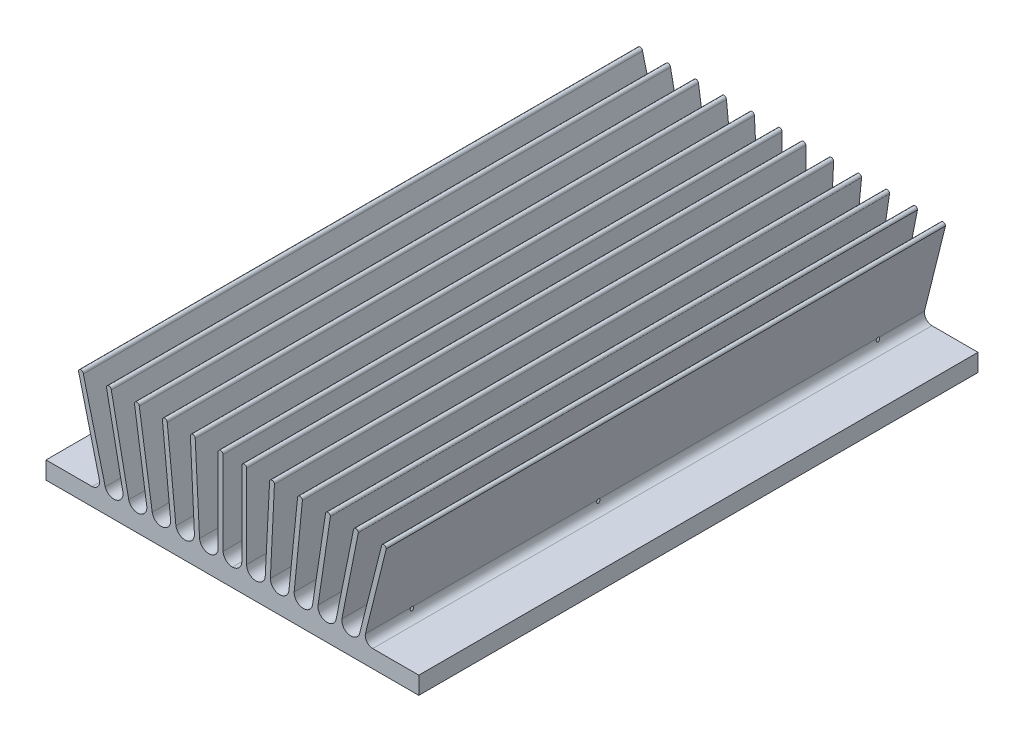
SolidWorks part; units mm, degrees
ref_plane "Front" through (0, 0, 0) normal (0, 0, 1) x (1, 0, 0)
ref_plane "Top" through (0, 0, 0) normal (0, 1, 0) x (1, 0, 0)
ref_plane "Right" through (0, 0, 0) normal (1, 0, 0) x (0, 0, -1)
sketch "Sketch1" plane through (0, 0, 0) normal (0, 0, 1) x (1, 0, 0)
  line L0 (-50.8, 0) -> (0, 0)
  line L3 (-50.8, 0) -> (-50.8, 4.7752)
  line L4 (-50.8, 4.7752) -> (-38.2296, 4.7752)
  line L5 (-41.9354, 30.1498) -> (-36.2408, 7.2569)
  line L6 (-40.6146, 30.1498) -> (-34.659, 6.4933)
  line L7 (-34.3154, 30.1498) -> (-29.8295, 7.5733)
  line L8 (-2.5527, 30.1508) -> (-2.5527, 7.3163)
  line L9 (0, 0) -> (0, 4.8796)
  line L10 (-32.9946, 30.1498) -> (-28.2534, 6.6437)
  line L11 (-26.6954, 30.1498) -> (-23.3483, 7.6331)
  line L12 (-25.3746, 30.1498) -> (-21.8459, 6.8815)
  line L13 (-19.0754, 30.1498) -> (-16.8368, 7.4459)
  line L14 (-17.7546, 30.1498) -> (-15.3936, 6.9122)
  line L22 (-3.8735, 30.1508) -> (-3.8735, 7.4254)
  line L28 (-11.4554, 30.1498) -> (-10.3495, 7.371)
  line L29 (-10.1346, 30.1498) -> (-8.9496, 7.1637)
  arc A0 (-40.6146, 30.1498) -> (-41.9354, 30.1498) centre (-41.275, 30.1498) ccw
  arc A1 (-32.9946, 30.1498) -> (-34.3154, 30.1498) centre (-33.655, 30.1498) ccw
  arc A2 (-25.3746, 30.1498) -> (-26.6954, 30.1498) centre (-26.035, 30.1498) ccw
  arc A3 (-17.7546, 30.1498) -> (-19.0754, 30.1498) centre (-18.415, 30.1498) ccw
  arc A4 (-10.1346, 30.1498) -> (-11.4554, 30.1498) centre (-10.795, 30.1498) ccw
  arc A5 (-2.5527, 30.1508) -> (-3.8735, 30.1508) centre (-3.2131, 30.1508) ccw
  arc A6 (-36.2408, 7.2569) -> (-38.2296, 4.7752) centre (-38.2866, 6.8586) cw
  arc A7 (-28.2534, 6.6437) -> (-23.3483, 7.6331) centre (-25.8209, 7.238) ccw
  arc A8 (-21.8459, 6.8815) -> (-16.8368, 7.4459) centre (-19.3576, 7.3081) ccw
  arc A9 (-15.3936, 6.9122) -> (-10.3495, 7.371) centre (-12.8923, 7.3696) ccw
  arc A10 (-8.9496, 7.1637) -> (-3.8735, 7.4254) centre (-6.4155, 7.3708) ccw
  arc A11 (-2.5527, 7.3163) -> (0, 4.8796) centre (0.0476, 7.4849) ccw
  arc A12 (-34.659, 6.4933) -> (-29.8295, 7.5733) centre (-32.2943, 7.2569) ccw
  dimension "D14" = 1.3208
  dimension "D15" = 1.3208
  dimension "D16" = 1.3208
  dimension "D17" = 1.3208
  dimension "D18" = 1.3208
  dimension "D19" = 1.3208
  dimension "D1" = 4.7752
  dimension "D3" = 50.8
extrude "Base-Extrude" add sketch "Sketch1" against normal blind 152.4
mirror "Mirror1" about plane through (0, 0, 0) normal (1, 0, 0) of "Base-Extrude"
hole_wizard "#4-40 Tapped Hole1" positions "3DSketch1" profile "Sketch6" tap size "#4-40" standard "Ansi Inch"
sketch3d "3DSketch1"
  line L0 (-50.8, 0, -152.4) -> (-50.8, 0, 0) construction
  line L1 (-50.8, 0, -152.4) -> (50.8, 0, -152.4) construction
  point P0 (-30.48, 0, -133.35)
  dimension "D1" = 20.32
  dimension "D2" = 19.05
sketch "Sketch6" plane through (-30.48, 0, -133.35) normal (1, 0, 0) x (0, 0, -1)
  line L0 (0, 0) -> (0, 8.6294)
  line L1 (0, 8.6294) -> (1.1303, 7.9502)
  line L2 (1.1303, 7.9502) -> (1.1303, 0)
  line L5 (1.1303, 0) -> (0, 0)
  line L10 (0, 8.6294) -> (-1.1303, 7.9502) construction
  line L11 (0, -6.35) -> (0, 107.95) construction
  dimension "Tap Drill Dia." = 2.2606
  dimension "Tap Drill Depth" = 7.9502
  dimension "Drill Angle" = 118
cosmetic thread "Hole Thread1" parameters "D1"=4.572, "D2"=2.8448
pattern_linear "LPattern10" count 2 spacing 60.96 along (1, 0, 0) count 2 spacing 114.3 along (0, 0, 1) of "#4-40 Tapped Hole1"
hole_wizard "#6-32 Tapped Hole1" positions "3DSketch2" profile "Sketch7" tap size "#6-32" standard "Ansi Inch"
sketch3d "3DSketch2"
  line L0 (-50.8, 0, -152.4) -> (-50.8, 0, 0) construction
  line L1 (-50.8, 0, -152.4) -> (50.8, 0, -152.4) construction
  point P0 (-34.925, 0, -139.7)
  point P2 (34.925, 0, -139.7)
  point P4 (34.925, 0, -63.5)
  point P6 (-34.925, 0, -63.5)
  point P8 (-34.925, 0, -12.7)
  point P10 (34.925, 0, -12.7)
  dimension "D1" = 15.875
  dimension "D2" = 69.85
  dimension "D3" = 12.7
  dimension "D4" = 12.7
  dimension "D5" = 15.875
  dimension "D6" = 69.85
  dimension "D7" = 76.2
  dimension "D8" = 76.2
  dimension "D9" = 127
  dimension "D10" = 15.875
  dimension "D11" = 69.85
  dimension "D12" = 127
sketch "Sketch7" plane through (-34.925, 0, -139.7) normal (1, 0, 0) x (0, 0, -1)
  line L0 (0, 0) -> (0, 8.7629)
  line L1 (0, 8.7629) -> (1.3525, 7.9502)
  line L2 (1.3525, 7.9502) -> (1.3525, 0)
  line L5 (1.3525, 0) -> (0, 0)
  line L10 (0, 8.7629) -> (-1.3526, 7.9502) construction
  line L11 (0, -6.35) -> (0, 107.95) construction
  dimension "Tap Drill Dia." = 2.7051
  dimension "Tap Drill Depth" = 7.9502
  dimension "Drill Angle" = 118
cosmetic thread "Hole Thread2" parameters "D1"=4.7752, "D2"=3.5052
cosmetic thread "Hole Thread3" parameters "D1"=4.7752, "D2"=3.5052
cosmetic thread "Hole Thread4" parameters "D1"=4.7752, "D2"=3.5052
cosmetic thread "Hole Thread5" parameters "D1"=4.7752, "D2"=3.5052
cosmetic thread "Hole Thread6" parameters "D1"=4.7752, "D2"=3.5052
cosmetic thread "Hole Thread7" parameters "D1"=4.7752, "D2"=3.5052
hole_wizard "#4-40 Tapped Hole2" positions "3DSketch4" profile "Sketch10" tap size "#4-40" standard "Ansi Inch"
sketch3d "3DSketch4"
  line L0 (-50.8, 0, -152.4) -> (50.8, 0, -152.4) construction
  line L1 (-50.8, 0, -152.4) -> (-50.8, 0, 0) construction
  point P0 (-34.925, 0, -32.385)
  point P2 (-26.67, 0, -43.18)
  point P4 (26.67, 0, -109.22)
  point P6 (34.925, 0, -120.015)
  dimension "D1" = 109.22
  dimension "D2" = 43.18
  dimension "D3" = 32.385
  dimension "D4" = 120.015
  dimension "D5" = 15.875
  dimension "D6" = 85.725
  dimension "D7" = 77.47
  dimension "D8" = 24.13
sketch "Sketch10" plane through (-34.925, 0, -32.385) normal (1, 0, 0) x (0, 0, -1)
  line L0 (0, 0) -> (0, 8.6294)
  line L1 (0, 8.6294) -> (1.1303, 7.9502)
  line L2 (1.1303, 7.9502) -> (1.1303, 0)
  line L5 (1.1303, 0) -> (0, 0)
  line L10 (0, 8.6294) -> (-1.1303, 7.9502) construction
  line L11 (0, -6.35) -> (0, 107.95) construction
  dimension "Tap Drill Dia." = 2.2606
  dimension "Tap Drill Depth" = 7.9502
  dimension "Drill Angle" = 118
cosmetic thread "Hole Thread8" parameters "D1"=4.7752, "D2"=2.8448
cosmetic thread "Hole Thread9" parameters "D1"=4.7752, "D2"=2.8448
cosmetic thread "Hole Thread10" parameters "D1"=4.7752, "D2"=2.8448
cosmetic thread "Hole Thread11" parameters "D1"=4.7752, "D2"=2.8448
hole_wizard "#4-40 Tapped Hole5" positions "Sketch17" profile "Sketch16" tap size "#4-40" standard "Ansi Inch"
sketch "Sketch17" plane through (0, 0, 0) normal (0, -1, 0) x (1, 0, 0)
  line L0 (-50.8, -152.4) -> (-50.8, 0) construction
  line L1 (-50.8, -152.4) -> (50.8, -152.4) construction
  point P0 (-34.925, -53.975)
  dimension "D1" = 15.875
  dimension "D2" = 98.425
sketch "Sketch16" plane through (-34.925, 0, -53.975) normal (1, 0, 0) x (0, 0, -1)
  line L0 (0, 0) -> (0, 8.6294)
  line L1 (0, 8.6294) -> (1.1303, 7.9502)
  line L2 (1.1303, 7.9502) -> (1.1303, 0)
  line L5 (1.1303, 0) -> (0, 0)
  line L10 (0, 8.6294) -> (-1.1303, 7.9502) construction
  line L11 (0, -6.35) -> (0, 107.95) construction
  dimension "Tap Drill Dia." = 2.2606
  dimension "Tap Drill Depth" = 7.9502
  dimension "Drill Angle" = 118
cosmetic thread "Hole Thread14" parameters "D1"=4.7752, "D2"=2.8448
